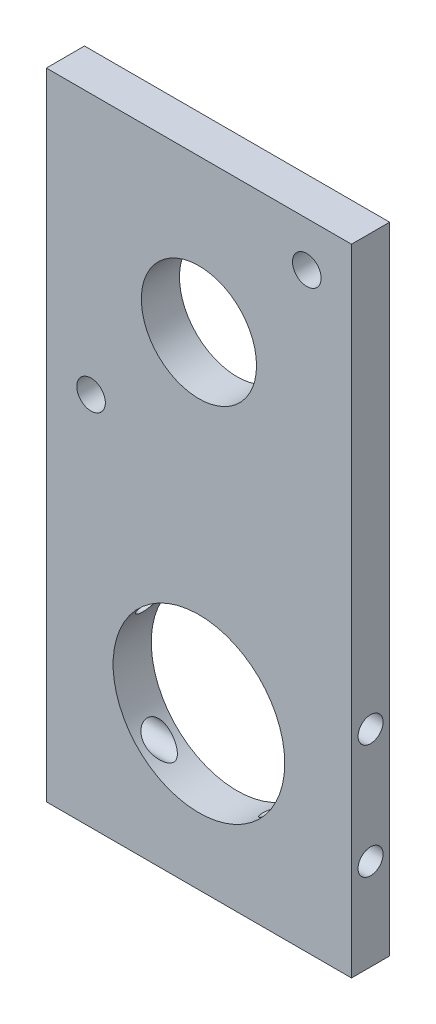
SolidWorks part; units mm, degrees
ref_plane "Front Plane" through (0, 0, 0) normal (0, 0, 1) x (1, 0, 0)
ref_plane "Top Plane" through (0, 0, 0) normal (0, 1, 0) x (1, 0, 0)
ref_plane "Right Plane" through (0, 0, 0) normal (1, 0, 0) x (0, 0, -1)
sketch "Sketch2" plane through (0, 0, 0) normal (0, 0, 1) x (1, 0, 0)
  line L0 (0, -25.4) -> (0, -29.6) construction
  line L3 (25.4, -80.4) -> (-25.4, -80.4)
  line L27 (25.4, 25.4) -> (-25.4, 25.4)
  line L28 (-25.4, 25.4) -> (-25.4, -80.4)
  line L29 (25.4, 25.4) -> (25.4, -80.4)
  line L30 (17.9605, 17.9605) -> (-17.9605, -17.9605) construction
  line L31 (0, 25.4) -> (0, -80.4) construction
  circle A7 centre (0, 0) radius 9.5885
  circle A12 centre (0, -55) radius 14.2875
  circle A15 centre (-17.9605, -17.9605) radius 2.3812
  circle A19 centre (17.9605, 17.9605) radius 2.3813
  circle A30 centre (0, -55) radius 25.4 construction
  circle A31 centre (0, 0) radius 25.4 construction
  point P4 (0, -27.5)
  point P11 (0, -80.4)
  point P14 (0, 25.4)
  point P16 (0, 0)
  dimension "D3" = 28.575
  dimension "D5" = 50.8
  dimension "D2" = 4.7625
  dimension "D7" = 19.177
  dimension "D6" = 55
  dimension "D1" = 50.8
  dimension "D4" = 45
extrude "Boss-Extrude1" add sketch "Sketch2" along normal blind 6.35
sketch "Sketch6" plane through (25.4, 0, 0) normal (1, 0, 0) x (0, 0, -1)
  line L0 (-3.175, -80.4) -> (-3.175, 25.4) construction
  line L1 (-6.35, -80.4) -> (0, -80.4) construction
  line L2 (-6.35, 25.4) -> (0, 25.4) construction
  circle A0 centre (-3.175, -65.16) radius 2.0828
  circle A1 centre (-3.175, -46.11) radius 2.0828
  dimension "D2" = 4.1656
  dimension "D3" = 15.24
  dimension "D1" = 19.05
extrude "Cut-Extrude1" cut sketch "Sketch6" against normal through all
equation "\"Pulley Teeth\"= 24"
equation "\"Belt Teeth\"= 46"
equation "\"Leftover Teeth\"= \"Belt Teeth\" - \"Pulley Teeth\""
equation "\"teeth size\"= 5mm"
equation "\"length\"= ( \"Leftover Teeth\" * \"teeth size\" ) / 2"
equation "\"D6@Sketch2\"=\"length\""
equation "\"belt size\"= ( \"Belt Teeth\" * \"teeth size\" )"
equation "\"belrt size\"= 220mm"
equation "\"blt\"= \"belrt size\" / \"teeth size\""
